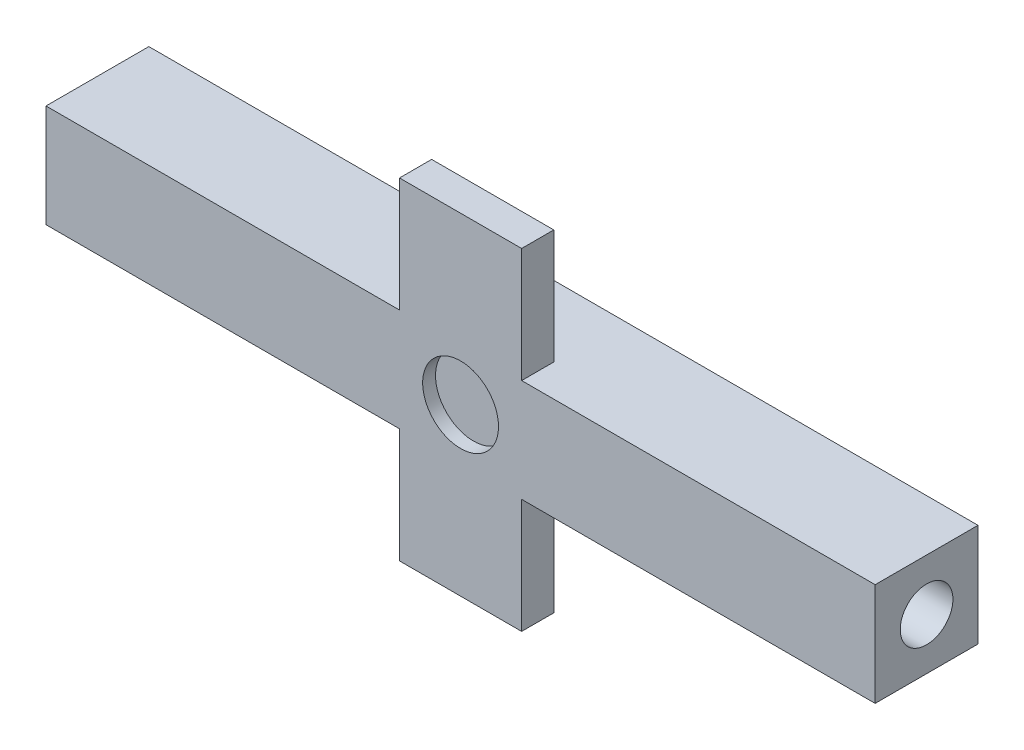
SolidWorks part; units mm, degrees
ref_plane "Front Plane" through (0, 0, 0) normal (0, 0, 1) x (1, 0, 0)
ref_plane "Top Plane" through (0, 0, 0) normal (0, 1, 0) x (1, 0, 0)
ref_plane "Right Plane" through (0, 0, 0) normal (1, 0, 0) x (0, 0, -1)
sketch "Sketch1" plane through (0, 0, 0) normal (1, 0, 0) x (0, 0, -1)
  line L1 (0, 0) -> (10.16, 0)
  line L2 (0, 0) -> (0, 10.16)
  line L3 (0, 10.16) -> (10.16, 10.16)
  line L4 (10.16, 0) -> (10.16, 10.16)
  dimension "D1" = 10.16
  dimension "D2" = 10.16
extrude "Boss-Extrude1" add sketch "Sketch1" along normal blind 81.915
ref_plane "Plane1" through (40.9575, 0, 0) normal (1, 0, 0) x (0, 0, -1)
sketch "Sketch6" plane through (81.915, 0, 0) normal (1, 0, 0) x (0, 0, -1)
  circle A0 centre (5.08, 5.08) radius 2.4765
  dimension "D1" = 4.953
sketch "Sketch10" plane through (81.915, 0, 0) normal (1, 0, 0) x (0, 0, -1)
  circle A0 centre (5.08, 5.08) radius 2.6035
  dimension "D1" = 5.207
extrude "Cut-Extrude6" cut sketch "Sketch10" against normal through all
sketch "Sketch11" plane through (0, 0, 0) normal (0, 0, 1) x (1, 0, 0)
  line L0 (81.915, 5.08) -> (0, 5.08) construction
  line L1 (81.915, 10.16) -> (81.915, 0) construction
  line L2 (0, 10.16) -> (0, 0) construction
  circle A2 centre (40.9575, 5.08) radius 3.7465
extrude "Cut-Extrude7" cut sketch "Sketch11" against normal blind 1.27
sketch "Sketch12" plane through (0, 0, 0) normal (0, -1, 0) x (1, 0, 0)
  line L0 (81.915, 0) -> (0, 0) construction
  line L1 (46.99, 0) -> (34.925, 0)
  line L2 (46.99, 0) -> (46.99, -3.175)
  line L3 (46.99, -3.175) -> (34.925, -3.175)
  line L4 (34.925, 0) -> (34.925, -3.175)
  line L5 (0, 0) -> (0, -10.16) construction
  line L6 (81.915, -7.5565) -> (81.915, -2.6035) construction
  dimension "D1" = 34.925
  dimension "D2" = 12.065
  dimension "D3" = 34.925
  dimension "D4" = 3.175
extrude "Boss-Extrude4" add sketch "Sketch12" along normal blind 11.303
sketch "Sketch13" plane through (0, 10.16, 0) normal (0, 1, 0) x (1, 0, 0)
  line L0 (81.915, 0) -> (0, 0) construction
  line L1 (46.99, 0) -> (34.925, 0)
  line L2 (46.99, 0) -> (46.99, 3.175)
  line L3 (46.99, 3.175) -> (34.925, 3.175)
  line L4 (34.925, 0) -> (34.925, 3.175)
  line L5 (81.915, 10.16) -> (81.915, 0) construction
  line L6 (0, 10.16) -> (0, 0) construction
  dimension "D1" = 12.065
  dimension "D2" = 34.925
  dimension "D3" = 34.925
extrude "Boss-Extrude5" add sketch "Sketch13" along normal blind 11.303
